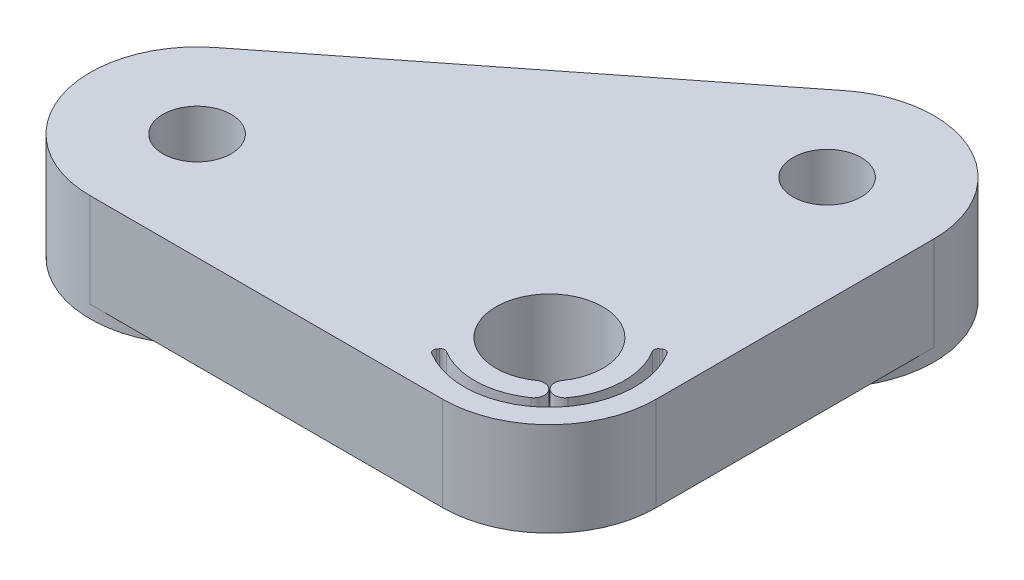
SolidWorks part; units mm, degrees
ref_plane "Front" through (0, 0, 0) normal (0, 0, 1) x (1, 0, 0)
ref_plane "Top" through (0, 0, 0) normal (0, 1, 0) x (1, 0, 0)
ref_plane "Right" through (0, 0, 0) normal (1, 0, 0) x (0, 0, -1)
sketch "Sketch1" plane through (0, 0, 0) normal (0, 1, 0) x (1, 0, 0)
  line L0 (0, 0) -> (16.5, 0) construction
  line L1 (16.5, 0) -> (0, 13) construction
  line L2 (0, 13) -> (0, 0) construction
  line L3 (-5, -5) -> (30.9254, -5)
  line L4 (30.9254, -5) -> (-5, 23.3048)
  line L5 (-5, 23.3048) -> (-5, -5)
  circle A0 centre (16.5, 0) radius 1.6
  circle A1 centre (0, 0) radius 2.5
  circle A2 centre (0, 13) radius 1.6
  dimension "D3" = 5
  dimension "D4" = 3.2
  dimension "D1" = 16.5
  dimension "D2" = 13
  dimension "D5" = 5
extrude "Boss-Extrude1" add sketch "Sketch1" along normal blind 1.57
fillet "Fillet1" radius 5 3 edges at (-5, 0.785, -23.3048) (-5, 0.785, 5) (30.9254, 0.785, 5)
other "Move Face1" [suppressed] parameters "D1"=0.0762
sketch "Sketch2" plane through (0, 1.57, 0) normal (0, 1, 0) x (1, 0, 0)
  line L3 (19.5944, 3.9275) -> (3.0944, 16.9275)
  line L4 (-5, 13) -> (-5, 0)
  line L5 (0, -5) -> (16.5, -5)
  line L6 (19.5944, 3.9275) -> (3.0944, 16.9275)
  line L7 (-5, 13) -> (-5, 0)
  line L8 (0, -5) -> (16.5, -5)
  circle A0 centre (0, 0) radius 2.5 construction
  circle A1 centre (16.5, 0) radius 1.6 construction
  circle A2 centre (0, 13) radius 1.6 construction
  arc A3 (3.0944, 16.9275) -> (-5, 13) centre (0, 13) ccw
  arc A4 (-5, 0) -> (0, -5) centre (0, 0) ccw
  arc A5 (16.5, -5) -> (19.5944, 3.9275) centre (16.5, 0) ccw
  arc A6 (3.0944, 16.9275) -> (-5, 13) centre (0, 13) ccw
  arc A7 (-5, 0) -> (0, -5) centre (0, 0) ccw
  arc A8 (16.5, -5) -> (19.5944, 3.9275) centre (16.5, 0) ccw
  circle A9 centre (0, 0) radius 2.5
  circle A10 centre (16.5, 0) radius 1.6
  circle A11 centre (0, 13) radius 1.6
  dimension "D1" = 0
extrude "Boss-Extrude2" add sketch "Sketch2" along normal blind 2.83
sketch "Sketch3" plane through (0, 0, 0) normal (0, -1, 0) x (1, 0, 0)
  circle A0 centre (16.5, 0) radius 5
  circle A1 centre (0, -13) radius 5
  circle A2 centre (0, -13) radius 1.6 construction
  circle A3 centre (16.5, 0) radius 1.6 construction
  circle A4 centre (0, -13) radius 1.6
  circle A5 centre (16.5, 0) radius 1.6
  arc A6 (19.5944, -3.9275) -> (16.5, 5) centre (16.5, 0) ccw construction
  arc A7 (-5, -13) -> (3.0944, -16.9275) centre (0, -13) ccw construction
extrude "Boss-Extrude3" add sketch "Sketch3" along normal blind 0.6
sketch "Sketch4" plane through (0, 4.4, 0) normal (0, 1, 0) x (1, 0, 0)
  line B0 (1.7207, -2.4575) -> (0, 0) construction
  line B1 (2.1191, -3.0264) -> (2.1766, -3.1085)
  line B2 (-3.0264, 2.1191) -> (-3.1085, 2.1766)
  line B3 (-1.7207, -2.4575) -> (0, 0) construction
  arc B4 (2.1187, -3.3928) -> (-3.3928, 2.1187) centre (0, 0) cw
  arc B5 (-1.4339, -2.0479) -> (-2.0075, -2.867) centre (-1.7207, -2.4575) ccw
  arc B6 (-2.0075, -2.867) -> (1.8496, -2.9714) centre (0, 0) ccw
  arc B7 (-2.867, -2.0075) -> (-2.9714, 1.8496) centre (0, 0) cw
  arc B8 (-2.0479, -1.4339) -> (-2.867, -2.0075) centre (-2.4575, -1.7207) cw
  arc B9 (-1.4339, -2.0479) -> (-2.0479, -1.4339) centre (0, 0) cw
  arc B10 (2.1191, -3.0264) -> (1.8496, -2.9714) centre (1.9553, -3.1411) ccw
  arc B11 (2.1766, -3.1085) -> (2.1187, -3.3928) centre (2.0127, -3.2232) cw
  arc B12 (-3.1085, 2.1766) -> (-3.3928, 2.1187) centre (-3.2232, 2.0127) ccw
  arc B13 (-3.0264, 2.1191) -> (-2.9714, 1.8496) centre (-3.1411, 1.9553) cw
sketch_block_instance "5mm_bore_flexure_relief-1"
sketch_block "5mm_bore_flexure_relief" parameters "D4"=2.5, "D6"=0.2, "D1"=80, "D2"=0.5, "D3"=70, "D5"=1
extrude "Cut-Extrude1" cut sketch "Sketch4" against normal blind 10
sketch "Sketch5" plane through (9.4139, 0, -11.9484) normal (0.6189, 0, -0.7855) x (-0.7855, 0, -0.6189)
  line L0 (-12.9606, 0.6) -> (8.0453, 0.6) construction
  line L1 (-12.9606, 4.4) -> (-12.9606, 0) construction
  line L2 (8.0453, 0) -> (8.0453, 4.4) construction
  line L3 (-12.9606, 0) -> (8.0453, 0) construction
  text T0 "RCR-01" font "Century Gothic" height in points 12
  dimension "D1" = 0.6
extrude "Part Num Left" [suppressed] cut sketch "Sketch5" against normal blind 0.4
mirror "Mirror1" about plane through (-5, 1.57, -23.3048) normal (1, 0, 0) of bodies 106 104
delete or keep bodies "Body-Delete/Keep 1" type keep bodies bodies 105
sketch "Sketch6" plane through (-13.2439, 0, -16.8096) normal (-0.6189, 0, -0.7855) x (-0.7855, 0, 0.6189)
  line L0 (-0.1904, 0.6) -> (20.8155, 0.6) construction
  line L1 (-0.1904, 0) -> (-0.1904, 4.4) construction
  line L2 (20.8155, 4.4) -> (20.8155, 0) construction
  line L3 (20.8155, 0) -> (-0.1904, 0) construction
  text T0 "RCR-01" font "Century Gothic" height in points 12
  dimension "D1" = 0.6
extrude "Part Num Right" cut sketch "Sketch6" against normal blind 0.4
